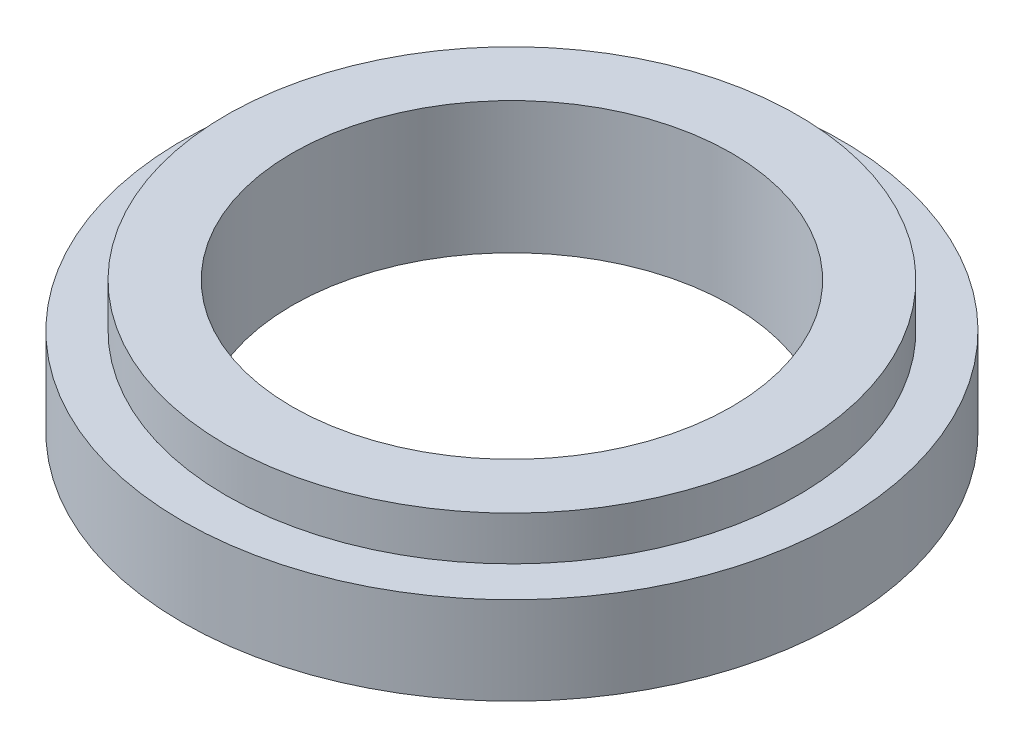
SolidWorks part; units mm, degrees
ref_plane "Front Plane" through (0, 0, 0) normal (0, 0, 1) x (1, 0, 0)
ref_plane "Top Plane" through (0, 0, 0) normal (0, 1, 0) x (1, 0, 0)
ref_plane "Right Plane" through (0, 0, 0) normal (1, 0, 0) x (0, 0, -1)
sketch "Sketch2" plane through (0, 0, 0) normal (0, 1, 0) x (1, 0, 0)
  circle A0 centre (0, 0) radius 2.5
  circle A1 centre (0, 0) radius 3.75
  dimension "D1" = 5
  dimension "D2" = 7.5
extrude "Boss-Extrude1" add sketch "Sketch2" along normal blind 1.5
sketch "Sketch3" plane through (0, 1.5, 0) normal (0, 1, 0) x (1, 0, 0)
  circle A0 centre (0, 0) radius 3.25
  circle A1 centre (0, 0) radius 3.75
  circle A2 centre (0, 0) radius 3.75 construction
  circle A3 centre (0, 0) radius 2.5 construction
  dimension "D1" = 0.75
extrude "Cut-Extrude1" cut sketch "Sketch3" against normal blind 0.5
